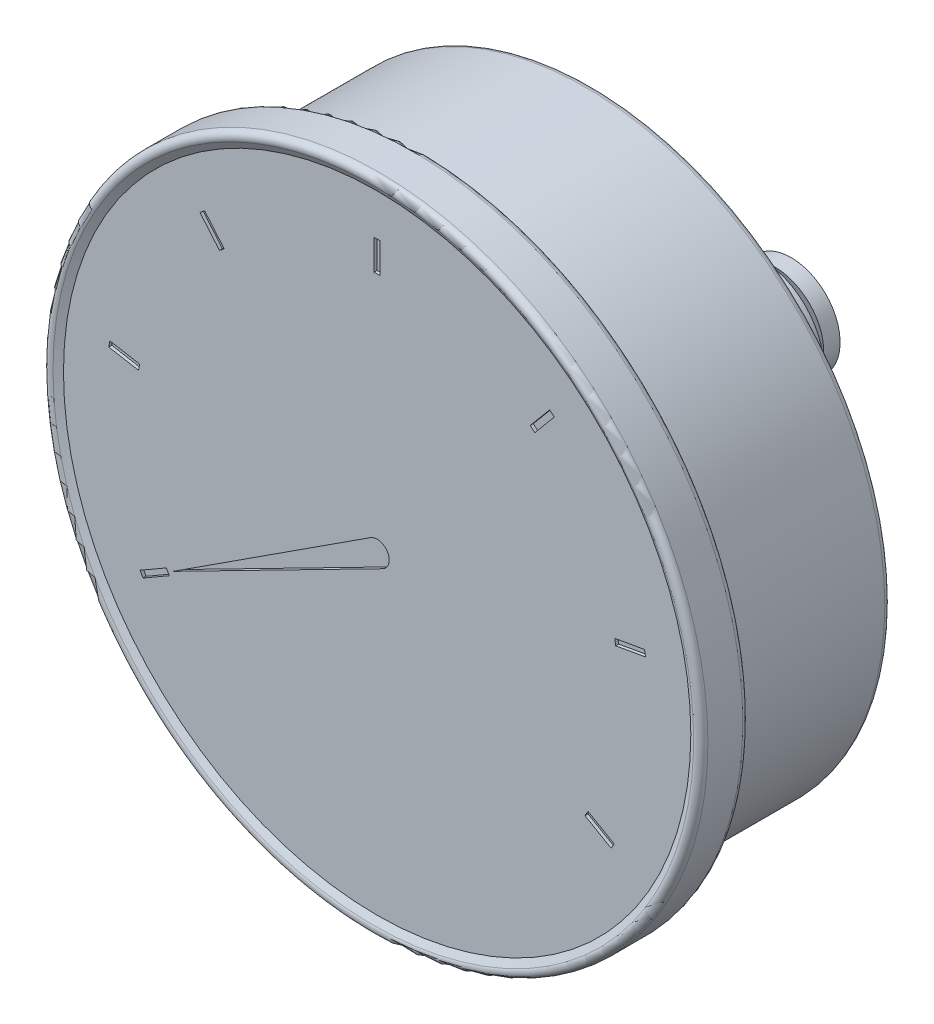
SolidWorks part; units mm, degrees
ref_plane "Horní" through (0, 0, 0) normal (0, 0, 1) x (1, 0, 0)
ref_plane "Přední" through (0, 0, 0) normal (0, 1, 0) x (1, 0, 0)
ref_plane "Pravá" through (0, 0, 0) normal (1, 0, 0) x (0, 0, -1)
sketch "Skica1" plane through (0, 0, 0) normal (1, 0, 0) x (0, 0, -1)
  line L0 (0, 54.5) -> (1.5, 51.9019)
  line L1 (0, 54.5) -> (8.5, 54.5)
  line L2 (70, 8.1) -> (67.3, 8.1)
  line L3 (67.3, 8.1) -> (65, 10.4)
  line L4 (37, 49.5) -> (37, 10.4)
  line L5 (70, 2.9) -> (72.7, 2.9)
  line L6 (72.7, 2.9) -> (72.7, 0)
  line L7 (72.7, 0) -> (1.5, 0)
  line L8 (0, 0) -> (-34.5616, 0) construction
  line L9 (37, 10.4) -> (65, 10.4)
  line L10 (1.5, 51.9019) -> (1.5, 0)
  line L11 (70, 8.1) -> (70, 2.9)
  line L12 (8.5, 54.5) -> (8.5, 49.5)
  line L13 (8.5, 49.5) -> (37, 49.5)
  dimension "D1" = 5.8
  dimension "D2" = 109
  dimension "D3" = 2.7
  dimension "D4" = 99
  dimension "D5" = 33
  dimension "D6" = 16.2
  dimension "D7" = 30
  dimension "D8" = 1.5
  dimension "D9" = 37
  dimension "D10" = 20.8
  dimension "D11" = 45
  dimension "D12" = 8.5
  dimension "D13" = 2.7
revolve "Rotovat1" add sketch "Skica1" angle 360 about L8
fillet "Zaoblit1" radius 1 3 edges at (-54.5, 0, 0) (-54.5, 0, -8.5) (-49.5, 0, -37)
sketch "Skica2" plane through (0, 0, -1.5) normal (0, 0, 1) x (1, 0, 0)
  line L0 (0, 45) -> (0, 0) construction
  line L3 (0.5, 40) -> (0.5, 45)
  line L4 (0.5, 40) -> (-0.5, 40)
  line L5 (0.5, 45) -> (-0.5, 45)
  line L6 (-0.5, 40) -> (-0.5, 45)
  dimension "D1" = 45
  dimension "D2" = 1
  dimension "D3" = 5
extrude "Odebrat vysunutím1" cut sketch "Skica2" against normal blind 0.5
pattern_circular "Kruhové pole1" count 9 over 360 about axis through (0, 0, 0) along (0, 0, 1) skipping 4, 5 of "Odebrat vysunutím1"
sketch "Skica3" plane through (0, 0, -1.5) normal (0, 0, 1) x (1, 0, 0)
  line L0 (-1.0875, 1.6785) -> (-33.775, -19.5)
  line L1 (-33.775, -19.5) -> (0.9099, -1.7811)
  line L2 (0, 0) -> (-33.775, -19.5) construction
  line L3 (-38.7211, -22.933) -> (-34.391, -20.433) construction
  arc A0 (0.9099, -1.7811) -> (-1.0875, 1.6785) centre (0, 0) ccw
  dimension "D1" = 2
  dimension "D2" = 39
extrude "Odebrat vysunutím2" cut sketch "Skica3" against normal blind 0.5
sketch "Skica4" plane through (0, 0, -37) normal (0, 0, -1) x (-1, 0, 0)
  line L1 (0, 12.7017) -> (-11, 6.3509)
  line L2 (-11, 6.3509) -> (-11, -6.3509)
  line L3 (-11, -6.3509) -> (0, -12.7017)
  line L4 (0, -12.7017) -> (11, -6.3509)
  line L5 (11, -6.3509) -> (11, 6.3509)
  line L6 (11, 6.3509) -> (0, 12.7017)
  circle A0 centre (0, 0) radius 11 construction
  dimension "D1" = 22
extrude "Přidat vysunutím1" add sketch "Skica4" against normal blind 3.5 from offset 13.5
pattern_linear "LinPole1" count 2 spacing 6.2 along (0, 0, 1) of "Přidat vysunutím1"
